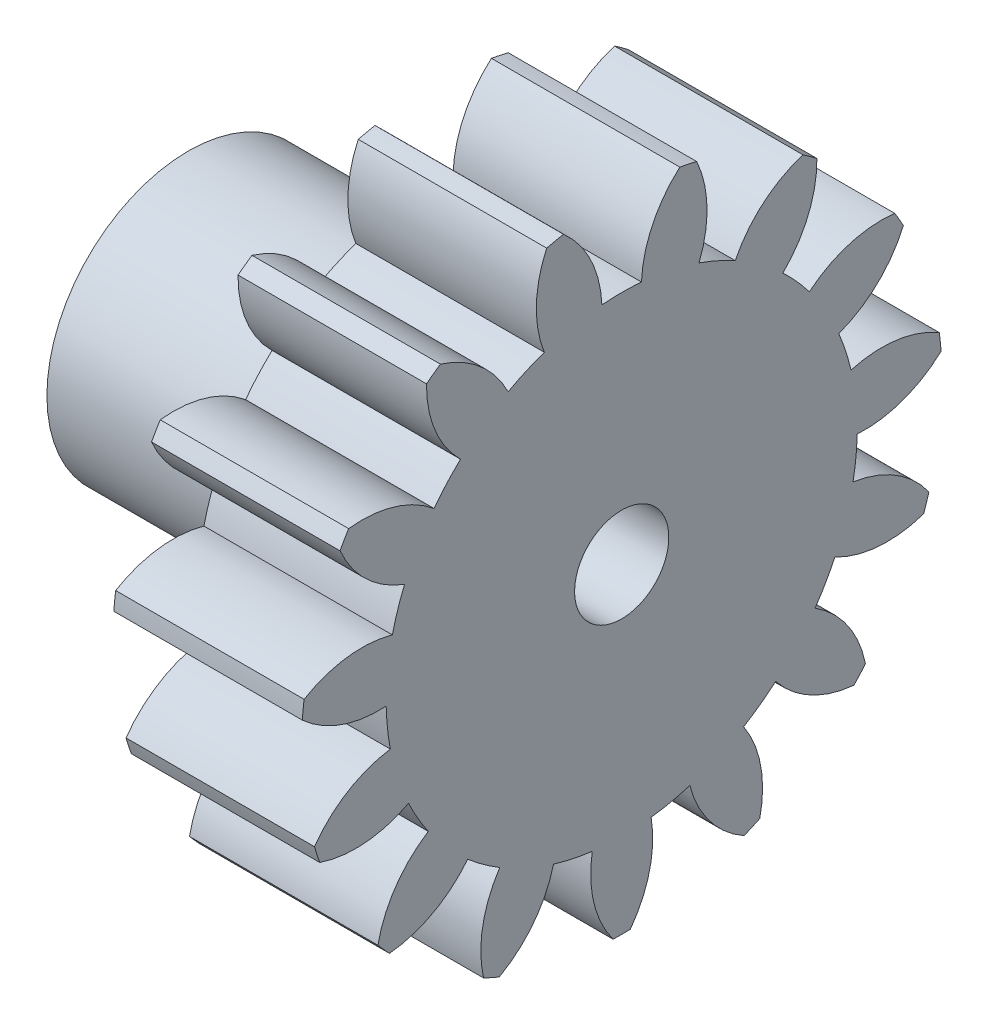
SolidWorks part; units mm, degrees
ref_plane "Plane1" through (0, 0, 0) normal (0, 0, 1) x (1, 0, 0)
ref_plane "Plane2" through (0, 0, 0) normal (0, 1, 0) x (1, 0, 0)
ref_plane "Plane3" through (0, 0, 0) normal (1, 0, 0) x (0, 0, -1)
sketch "HoldingSke" plane through (0, 0, 0) normal (0, 1, 0) x (1, 0, 0)
  line L0 (0, 0) -> (0.483, -0.1294)
  line L1 (-15, 0) -> (100, 0) construction
  line L2 (0, 0) -> (-2.1039, 2.3779)
  line L3 (0, 0) -> (-11.863, 4.5341)
  line L4 (0, 0) -> (8.3417, 2.2352)
  line L5 (0, 0) -> (-21.5499, -8.0375)
  line L6 (0, 0) -> (-8.2896, -5.593)
  line L7 (-2.1039, 2.3779) -> (2.8469, 24.8388)
  line L8 (-76.2, 54.61) -> (-75.3, 54.61)
  line L9 (-71.009, 38.7566) -> (-53.1078, 45.2721)
  line L10 (-76.2, 71.12) -> (104.1128, 71.12)
  line L11 (0, 0) -> (-10, 0)
  line L12 (-76.2, 101.6) -> (-76.133, 101.6)
  line L13 (24.9733, 27.94) -> (52.9518, 28.4284)
  line L14 (24.9733, 27.94) -> (24.9743, 27.94)
  line L15 (24.9733, 27.94) -> (100.4006, 29.5858)
  line L16 (-63.627, -2) -> (-12.827, -2)
  circle A0 centre (0, 0) radius 2.5
  circle A1 centre (0, 0) radius 7.5
  circle A2 centre (0, 0) radius 7.5
  circle A3 centre (0, 0) radius 2.5
  dimension "MHD" = 15
  dimension "Hub_dia" = 15
  dimension "Bore" = 5
  dimension "MBD" = 5
  dimension "Num_teeth" = 15
  dimension "Pitch" = 0.5
  dimension "Overall_len" = 23
  dimension "Show_teeth" = 15
  dimension "Thickness" = 10
  dimension "OAL" = 23.0001
  dimension "T_dim" = 0.9
  dimension "Ap" = 20
  dimension "H" = 19.05
  dimension "Pitch_radius" = 180.3128
  dimension "Width" = 10
  dimension "Backlash" = 0.067
  dimension "Addendum_fac" = 1
  dimension "Dedendum_fac" = 1.25
  dimension "Clearance_fac" = 0.25
  dimension "Dedendum_add" = 0.001
  dimension "Module" = 2
sketch "BasProSke" plane through (0, 0, 0) normal (0, 1, 0) x (1, 0, 0)
  line L0 (-10, 0) -> (60, 0) construction
  line L1 (0, 0) -> (0, 17)
  line L2 (0, 0) -> (10, 0)
  line L3 (10, 0) -> (10, 17)
  line L4 (10, 17) -> (0, 17)
  dimension "Thickness" = 10
  dimension "Diameter" = 34
revolve "Base-Revolve" add sketch "BasProSke" angle 360 about L0
sketch "TooCutSke" plane through (0, 0, 0) normal (1, 0, 0) x (0, 0, -1)
  line L1 (0, 0) -> (0, 107) construction
  line L2 (0, 0) -> (-1.6851, 14.905) construction
  line L3 (0, 0) -> (-6.2081, 29.2069) construction
  line L4 (-1.6851, 14.905) -> (-3.1041, 14.6034) construction
  arc A0 (1.0501, 12.4548) -> (-1.0501, 12.4548) centre (0, 0) ccw
  arc A1 (3.1109, 16.7388) -> (-3.1109, 16.7388) centre (0, 0) ccw
  circle A2 centre (0, 0) radius 15 construction
  circle A3 centre (0, 0) radius 14.0954 construction
  arc A4 (-1.0501, 12.4548) -> (-3.1109, 16.7388) centre (-7.045, 12.2085) ccw
  arc A5 (3.1109, 16.7388) -> (1.0501, 12.4548) centre (7.045, 12.2085) ccw
  dimension "Root_dia" = 24.998
  dimension "Overcut_dia" = 34.0508
  dimension "Pitch_dia" = 30
  dimension "Base_dia" = 28.1908
  dimension "Flank_rad" = 6
  dimension "Half_ang" = 12
  dimension "Half_CT" = 1.4507
extrude "ToothCut" cut sketch "TooCutSke" along normal through all
fillet "Breaks" [suppressed] radius 0.04
fillet "RootFillets" [suppressed] radius 0.501
pattern_circular "TeethCuts" count 15 every 24 about axis through (-10, 0, 0) along (1, 0, 0) of "ToothCut", "RootFillets", "Breaks"
sketch "HubNeaOneSke" plane through (0, 0, 0) normal (-1, 0, 0) x (0, 0, 1)
  circle A0 centre (0, 0) radius 7.5
  dimension "Diameter" = 15
extrude "HubNearOne" add sketch "HubNeaOneSke" along normal blind 13.0001
sketch "HubNeaBotSke" plane through (0, 0, 0) normal (-1, 0, 0) x (0, 0, 1)
  circle A0 centre (0, 0) radius 7.5
  dimension "Diameter" = 15
extrude "HubNearBoth" [suppressed] add sketch "HubNeaBotSke" along normal blind 6.5
ref_plane "FarPln" through (10, 0, 0) normal (1, 0, 0) x (0, 0, -1)
sketch "HubFarSke" plane through (10, 0, 0) normal (1, 0, 0) x (0, 0, -1)
  circle A0 centre (0, 0) radius 7.5
  dimension "Diameter" = 15
extrude "HubFar" [suppressed] add sketch "HubFarSke" along normal blind 6.5
sketch "BorSke" plane through (0, 0, 0) normal (1, 0, 0) x (0, 0, -1)
  circle A0 centre (0, 0) radius 2.5
  dimension "Diameter" = 5
extrude "Bore" cut sketch "BorSke" along normal mid plane 46.0001
sketch "KeySke" plane through (0, 0, 0) normal (1, 0, 0) x (0, 0, -1)
  line L0 (-1, 0) -> (-1, 3.4)
  line L1 (-1, 3.4) -> (1, 3.4)
  line L2 (1, 3.4) -> (1, 0)
  line L3 (0, 0) -> (0, 34) construction
  line L4 (-1, 0) -> (1, 0)
  dimension "Offset" = 3.4
  dimension "Width" = 2
extrude "Keyway" [suppressed] cut sketch "KeySke" along normal mid plane 46.0001
pattern_circular "Keyway2" [suppressed] count 2 every 90 about axis through (-10, 0, 0) along (1, 0, 0)
equation "' \"Module@HoldingSke\" = 6.35"
equation "' \"Num_teeth@HoldingSke\" = 12"
equation "' \"Ap@HoldingSke\" =  20"
equation "' \"Ap@HoldingSke\" = 20"
equation "' \"Width@HoldingSke\" = 0.5 * 25.4"
equation "' \"Hub_dia@HoldingSke\"= 1 * 25.4"
equation "' \"Hub_dia@HoldingSke\" = 1 * 25.4"
equation "' \"Overall_len@HoldingSke\" = 1.0 * 25.4"
equation "' \"Bore@HoldingSke\" = 0.75 * 25.4"
equation "' \"T_dim@HoldingSke\" = 0.1 * 25.4"
equation "' \"Width@KeySke\" = 0.25 * 25.4"
equation "' \"Show_teeth@HoldingSke\" = 13"
equation "' \"Backlash@HoldingSke\" = 0.009 * 25.4"
equation "' \"Addendum_fac@HoldingSke\" = 1.0"
equation "' \"Dedendum_fac@HoldingSke\" = 1.25"
equation "' \"Dedendum_add@HoldingSke\" = 0.00005 * 25.4"
equation "' \"Clearance_fac@HoldingSke\" = 0.25"
equation "\"Pitch@HoldingSke\" = 1 / \"Module@HoldingSke\""
equation "\"Overcut_dia@TooCutSke\" = (\"Num_teeth@HoldingSke\" + 2 * \"Addendum_fac@HoldingSke\") / \"Pitch@HoldingSke\" + 0.002 * 25.4"
equation "\"Pitch_dia@TooCutSke\" = \"Num_teeth@HoldingSke\" / \"Pitch@HoldingSke\""
equation "\"Base_dia@TooCutSke\" = \"Num_teeth@HoldingSke\" / \"Pitch@HoldingSke\" * cos((\"Ap@HoldingSke\"  * 3.14159265 / 180))"
equation "\"Root_dia@TooCutSke\" = (\"Num_teeth@HoldingSke\" + 2) / \"Pitch@HoldingSke\" - 2 * (\"Addendum_fac@HoldingSke\" + \"Dedendum_fac@HoldingSke\") / \"Pitch@HoldingSke\" - \"Dedendum_add@HoldingSke\" * 2"
equation "\"Half_ang@TooCutSke\" = 180 / \"Num_teeth@HoldingSke\""
equation "\"Half_CT@TooCutSke\" = \"Num_teeth@HoldingSke\" / \"Pitch@HoldingSke\" * sin((3.14159265 / 2 / \"Num_teeth@HoldingSke\")) / 2 - 7 * \"Backlash@HoldingSke\" / 4"
equation "\"Flank_rad@TooCutSke\" = \"Num_teeth@HoldingSke\" / \"Pitch@HoldingSke\" / 5"
equation "\"Radius@RootFillets\" = \"Clearance_fac@HoldingSke\" / \"Pitch@HoldingSke\" + \"Dedendum_add@HoldingSke\""
equation "\"Break_rad@Breaks\" = 0.02 / \"Pitch@HoldingSke\""
equation "\"Thickness@HoldingSke\" = \"Width@HoldingSke\""
equation "\"OAL@HoldingSke\" = \"Thickness@HoldingSke\""
equation "\"MHD@HoldingSke\" = (\"Num_teeth@HoldingSke\" + 2) / \"Pitch@HoldingSke\" - 2 * (\"Addendum_fac@HoldingSke\" + \"Dedendum_fac@HoldingSke\")  / \"Pitch@HoldingSke\" - \"Dedendum_add@HoldingSke\" * 2"
equation "\"MBD@HoldingSke\" = (\"Num_teeth@HoldingSke\" + 2) / \"Pitch@HoldingSke\" - 2 * (\"Addendum_fac@HoldingSke\" + \"Dedendum_fac@HoldingSke\")  / \"Pitch@HoldingSke\" - \"Dedendum_add@HoldingSke\" * 2 - 0.002 * 25.4"
equation "\"MHD@HoldingSke\" = ((sgn( \"MHD@HoldingSke\" - \"Hub_dia@HoldingSke\" )-1)*( \"MHD@HoldingSke\" - \"Hub_dia@HoldingSke\" ))/-2+ \"Hub_dia@HoldingSke\""
equation "\"MBD@HoldingSke\" = ((sgn( \"MBD@HoldingSke\" - \"Bore@HoldingSke\" )-1)*( \"MBD@HoldingSke\" - \"Bore@HoldingSke\" ))/-2+ \"Bore@HoldingSke\""
equation "\"OAL@HoldingSke\" = ((sgn( \"OAL@HoldingSke\" - \"Overall_len@HoldingSke\" )+1)*( \"OAL@HoldingSke\" - \"Overall_len@HoldingSke\" ))/2 + \"Overall_len@HoldingSke\" + 0.000002 * 25.4"
equation "\"Num_teeth@TeethCuts\" = int( \"Show_teeth@HoldingSke\" ) + 1"
equation "\"Num_teeth@TeethCuts\" = ((sgn( \"Num_teeth@TeethCuts\" - \"Num_teeth@HoldingSke\" )-1)*( \"Num_teeth@TeethCuts\" - \"Num_teeth@HoldingSke\" ))/-2+ \"Num_teeth@HoldingSke\""
equation "\"Num_teeth@TeethCuts\" = ((sgn( \"Num_teeth@TeethCuts\" - 2.0)+1)*( \"Num_teeth@TeethCuts\" - 2.0))/2 +2.0"
equation "\"Angle@TeethCuts\" = 360.0 / \"Num_teeth@HoldingSke\""
equation "\"Diameter@BasProSke\" = (\"Num_teeth@HoldingSke\" + 2 * \"Addendum_fac@HoldingSke\") / \"Pitch@HoldingSke\""
equation "\"Thickness@BasProSke\"  = \"Thickness@HoldingSke\""
equation "' \"Fillet_rad@BasProSke\" =  \"Thickness@HoldingSke\" * 0.05"
equation "' \"Fillet_rad@BasProSke\" = \"Thickness@HoldingSke\" * 0.05"
equation "\"MHD@HoldingSke\" = ((sgn( \"MHD@HoldingSke\" - \"Root_dia@TooCutSke\" )-1)*( \"MHD@HoldingSke\" - \"Root_dia@TooCutSke\" ))/-2+ \"Root_dia@TooCutSke\""
equation "\"Diameter@HubNeaOneSke\" = \"MHD@HoldingSke\""
equation "\"Length@HubNearOne\" = \"OAL@HoldingSke\" - \"Thickness@BasProSke\""
equation "\"Diameter@HubNeaBotSke\" = \"MHD@HoldingSke\""
equation "\"Length@HubNearBoth\" = ( \"OAL@HoldingSke\" - \"Thickness@BasProSke\" ) / 2.0"
equation "\"Thickness@FarPln\" = \"Thickness@BasProSke\""
equation "\"Diameter@HubFarSke\" = \"MHD@HoldingSke\""
equation "\"Length@HubFar\" = ( \"OAL@HoldingSke\" - \"Thickness@BasProSke\" ) / 2.0"
equation "\"Diameter@BorSke\" = \"MBD@HoldingSke\""
equation "\"D1@Bore\" = \"OAL@HoldingSke\" * 2.0"
equation "\"D1@Keyway\" = \"OAL@HoldingSke\" * 2.0"
equation "\"Offset@KeySke\" = \"T_dim@HoldingSke\" + \"MBD@HoldingSke\" / 2.0"
